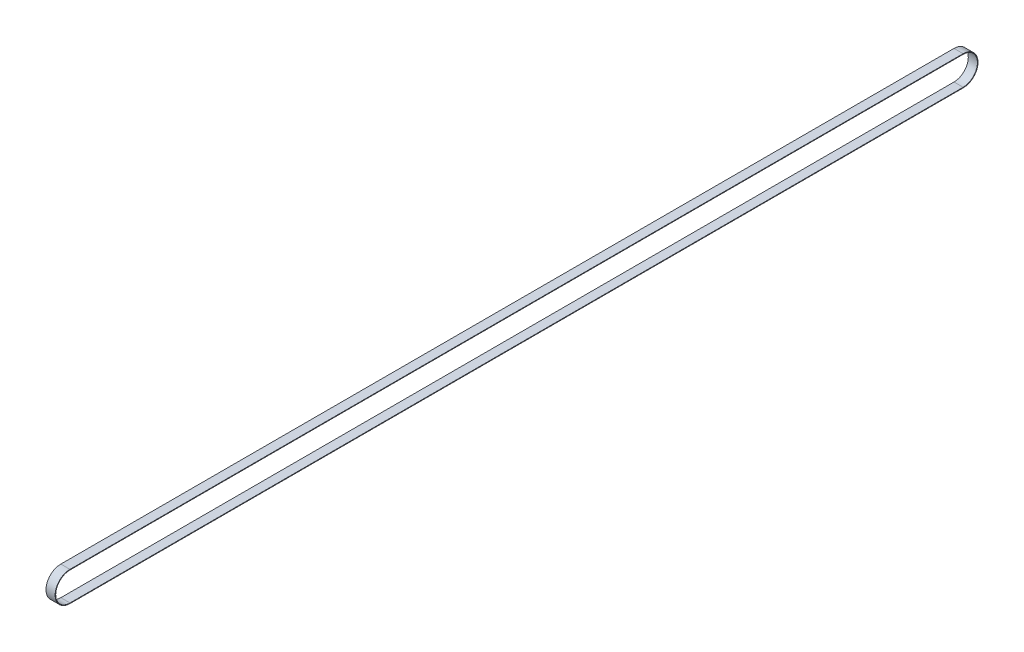
SolidWorks part; units mm, degrees
ref_plane "Front" through (0, 0, 0) normal (0, 0, 1) x (1, 0, 0)
ref_plane "Top" through (0, 0, 0) normal (0, 1, 0) x (1, 0, 0)
ref_plane "Right" through (0, 0, 0) normal (1, 0, 0) x (0, 0, -1)
sketch "Sketch1" plane through (0, 0, 0) normal (1, 0, 0) x (0, 0, -1)
  line L0 (0, 0) -> (1465, 0) construction
  line L1 (0, 23.4) -> (1465, 23.4)
  line L2 (0, -23.4) -> (1465, -23.4)
  line L3 (0, 0) -> (1465, 0) construction
  line L4 (0, 24.35) -> (1465, 24.35)
  line L5 (0, -24.35) -> (1465, -24.35)
  arc A0 (0, 23.4) -> (0, -23.4) centre (0, 0) ccw
  arc A1 (1465, -23.4) -> (1465, 23.4) centre (1465, 0) ccw
  arc A2 (0, 24.35) -> (0, -24.35) centre (0, 0) ccw
  arc A3 (1465, -24.35) -> (1465, 24.35) centre (1465, 0) ccw
  point P3 (732.5, 0)
  point P10 (732.5, 0)
  dimension "D2" = 46.8
  dimension "D3" = 48.7
  dimension "D1" = 1465
extrude "Boss-Extrude1" add sketch "Sketch1" against normal blind 15
